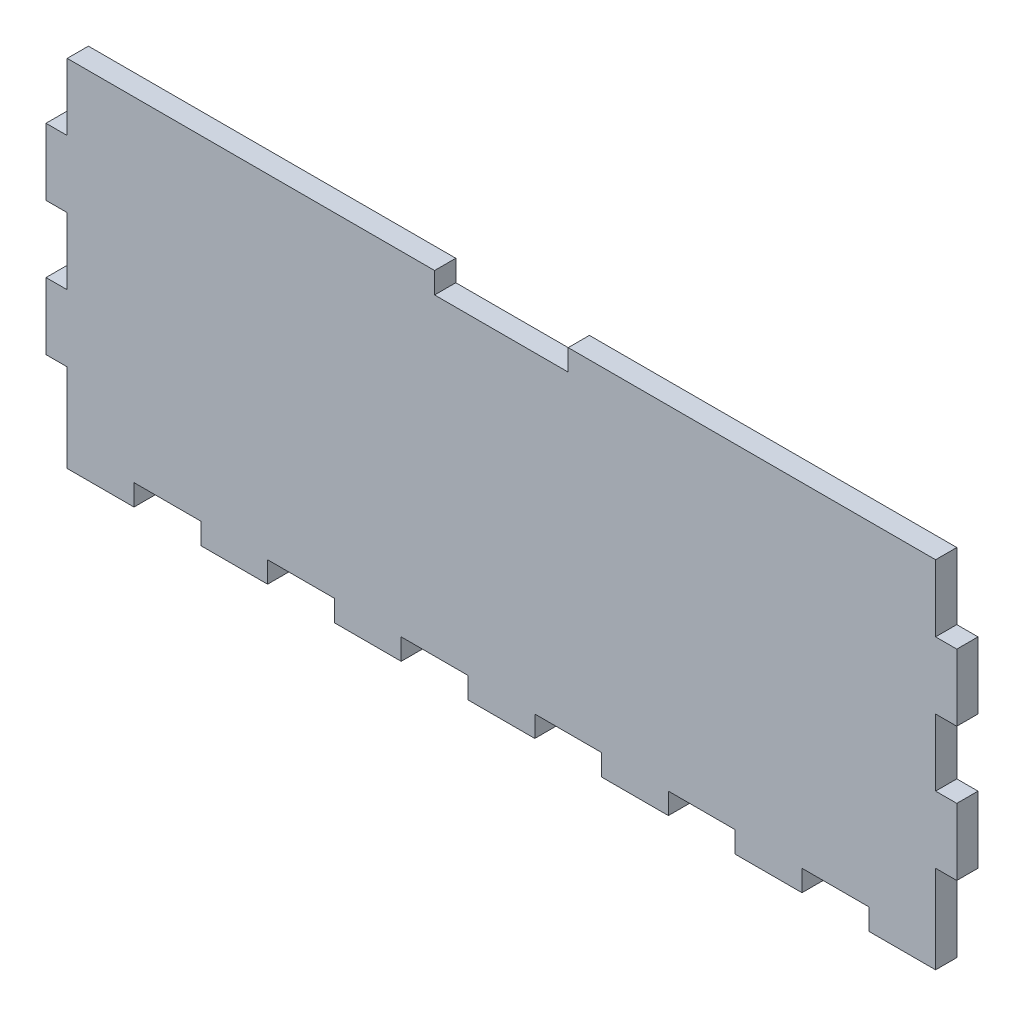
SolidWorks part; units mm, degrees
ref_plane "Plan de face" through (0, 0, 0) normal (0, 0, 1) x (1, 0, 0)
ref_plane "Plan de dessus" through (0, 0, 0) normal (0, 1, 0) x (1, 0, 0)
ref_plane "Plan de droite" through (0, 0, 0) normal (1, 0, 0) x (0, 0, -1)
sketch "Esquisse1" plane through (0, 0, 0) normal (0, 0, 1) x (1, 0, 0)
  line L1 (0, 0) -> (130, 0)
  line L2 (0, 0) -> (0, 50)
  line L3 (0, 50) -> (130, 50)
  line L4 (130, 0) -> (130, 50)
  dimension "D1" = 50
  dimension "D2" = 130
extrude "Boss.-Extru.1" add sketch "Esquisse1" along normal blind 3.175
sketch "Esquisse2" plane through (0, 0, 3.175) normal (0, 0, 1) x (1, 0, 0)
  line L0 (130, 0) -> (130, 50) construction
  line L1 (130, 40) -> (133.175, 40)
  line L2 (130, 40) -> (130, 30)
  line L3 (130, 30) -> (133.175, 30)
  line L4 (133.175, 40) -> (133.175, 30)
  line L5 (130, 50) -> (0, 50) construction
  line L6 (0, 50) -> (0, 0) construction
  line L7 (130, 20) -> (133.175, 20)
  line L8 (130, 20) -> (130, 10)
  line L9 (130, 10) -> (133.175, 10)
  line L10 (133.175, 20) -> (133.175, 10)
  line L11 (0, 40) -> (-3.175, 40)
  line L12 (0, 40) -> (0, 30)
  line L13 (0, 30) -> (-3.175, 30)
  line L14 (-3.175, 40) -> (-3.175, 30)
  line L16 (0, 20) -> (-3.175, 20)
  line L17 (0, 20) -> (0, 10)
  line L18 (0, 10) -> (-3.175, 10)
  line L19 (-3.175, 20) -> (-3.175, 10)
  dimension "D1" = 10
  dimension "D2" = 10
  dimension "D3" = 10
  dimension "D4" = 10
  dimension "D5" = 3.175
  dimension "D6" = 3.175
  dimension "D7" = 3.175
extrude "Boss.-Extru.2" add sketch "Esquisse2" against normal blind 3.175
sketch "Esquisse3" plane through (0, 0, 3.175) normal (0, 0, 1) x (1, 0, 0)
  line L0 (130, 50) -> (0, 50) construction
  line L1 (55, 50) -> (75, 50)
  line L2 (55, 50) -> (55, 46.825)
  line L3 (55, 46.825) -> (75, 46.825)
  line L4 (75, 50) -> (75, 46.825)
  line L5 (0, 50) -> (0, 40) construction
  line L6 (130, 40) -> (130, 50) construction
  dimension "D1" = 55
  dimension "D2" = 55
  dimension "D3" = 3.175
extrude "Enlèv. mat.-Extru.1" cut sketch "Esquisse3" against normal blind 3.175
sketch "Esquisse4" plane through (0, 0, 3.175) normal (0, 0, 1) x (1, 0, 0)
  line L1 (0, 0) -> (10, 0)
  line L2 (0, 0) -> (0, -3.175)
  line L3 (0, -3.175) -> (10, -3.175)
  line L4 (10, 0) -> (10, -3.175)
  dimension "D1" = 3.175
  dimension "D2" = 10
extrude "Boss.-Extru.3" add sketch "Esquisse4" against normal blind 3.175
pattern_linear "Répétition linéaire1" count 7 spacing 20 along (1, 0, 0) of "Boss.-Extru.3"
